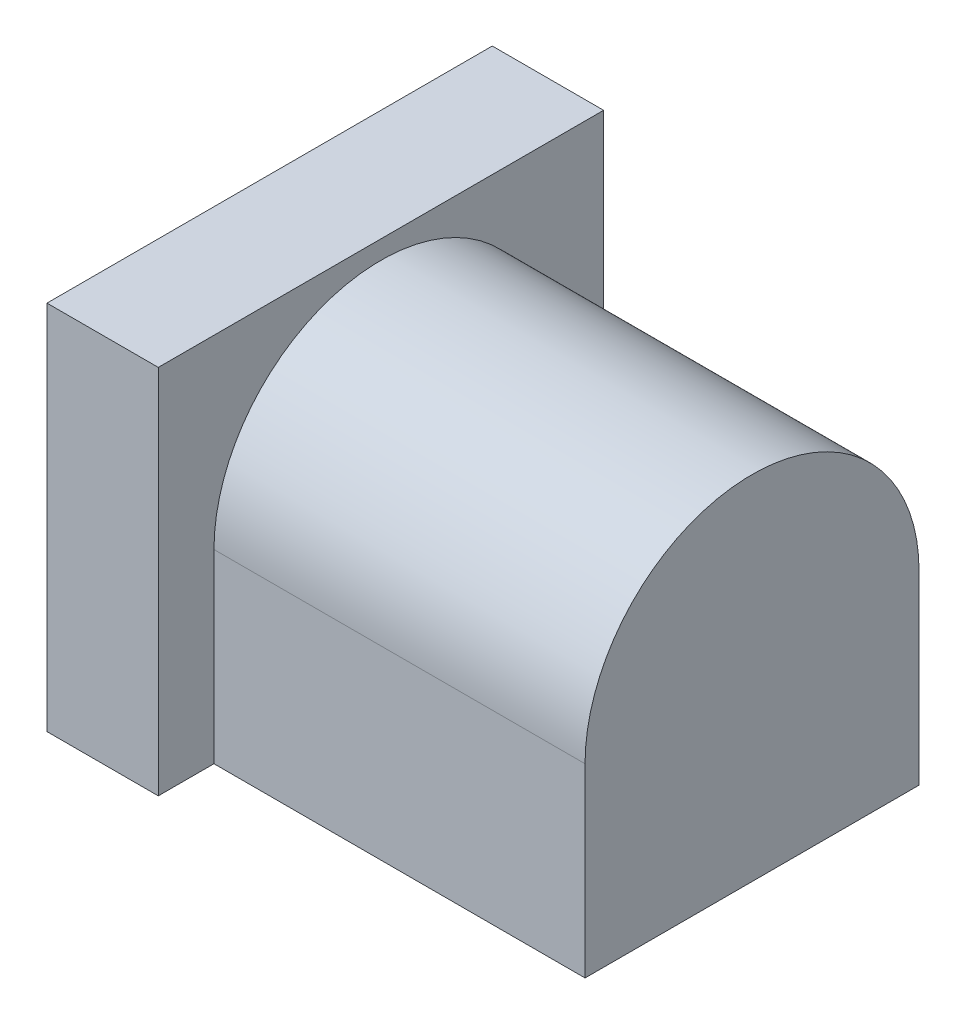
SolidWorks part; units mm, degrees
ref_plane "Front Plane" through (0, 0, 0) normal (0, 0, 1) x (1, 0, 0)
ref_plane "Top Plane" through (0, 0, 0) normal (0, 1, 0) x (1, 0, 0)
ref_plane "Right Plane" through (0, 0, 0) normal (1, 0, 0) x (0, 0, -1)
sketch "Sketch1" plane through (0, 0, 0) normal (1, 0, 0) x (0, 0, -1)
  line L0 (0, -38.1793) -> (0, -76.9131) construction
  line L1 (-4.5, -43.1793) -> (4.5, -43.1793)
  line L2 (-4.5, -43.1793) -> (-4.5, -38.1793)
  line L4 (4.5, -43.1793) -> (4.5, -38.1793)
  arc A0 (-4.5, -38.1793) -> (4.5, -38.1793) centre (0, -38.1793) cw
  dimension "D1" = 9
  dimension "D2" = 5
extrude "Boss-Extrude1" add sketch "Sketch1" along normal blind 10
sketch "Sketch2" plane through (0, 0, 0) normal (-1, 0, 0) x (0, 0, 1)
  line L0 (0, -31.3937) -> (0, -46.5445) construction
  line L1 (-6, -43.1793) -> (6, -43.1793)
  line L2 (-6, -43.1793) -> (-6, -33.1793)
  line L3 (-6, -33.1793) -> (6, -33.1793)
  line L4 (6, -43.1793) -> (6, -33.1793)
  dimension "D1" = 12
  dimension "D2" = 10
extrude "Boss-Extrude2" add sketch "Sketch2" along normal blind 3
sketch "Sketch3" plane through (-3, 0, 0) normal (-1, 0, 0) x (0, 0, 1)
  circle A0 centre (0, -38.1793) radius 3
  dimension "D1" = 6
extrude "Cut-Extrude1" cut sketch "Sketch3" against normal blind 12
sketch "Sketch4" plane through (9, 0, 0) normal (-1, 0, 0) x (0, 0, 1)
  circle A0 centre (0, -38.1793) radius 0.5
  dimension "D1" = 1
extrude "Boss-Extrude3" add sketch "Sketch4" along normal blind 10
fillet "Fillet6" radius 0.5 1 edges at (-1, -38.1793, 0.5)
